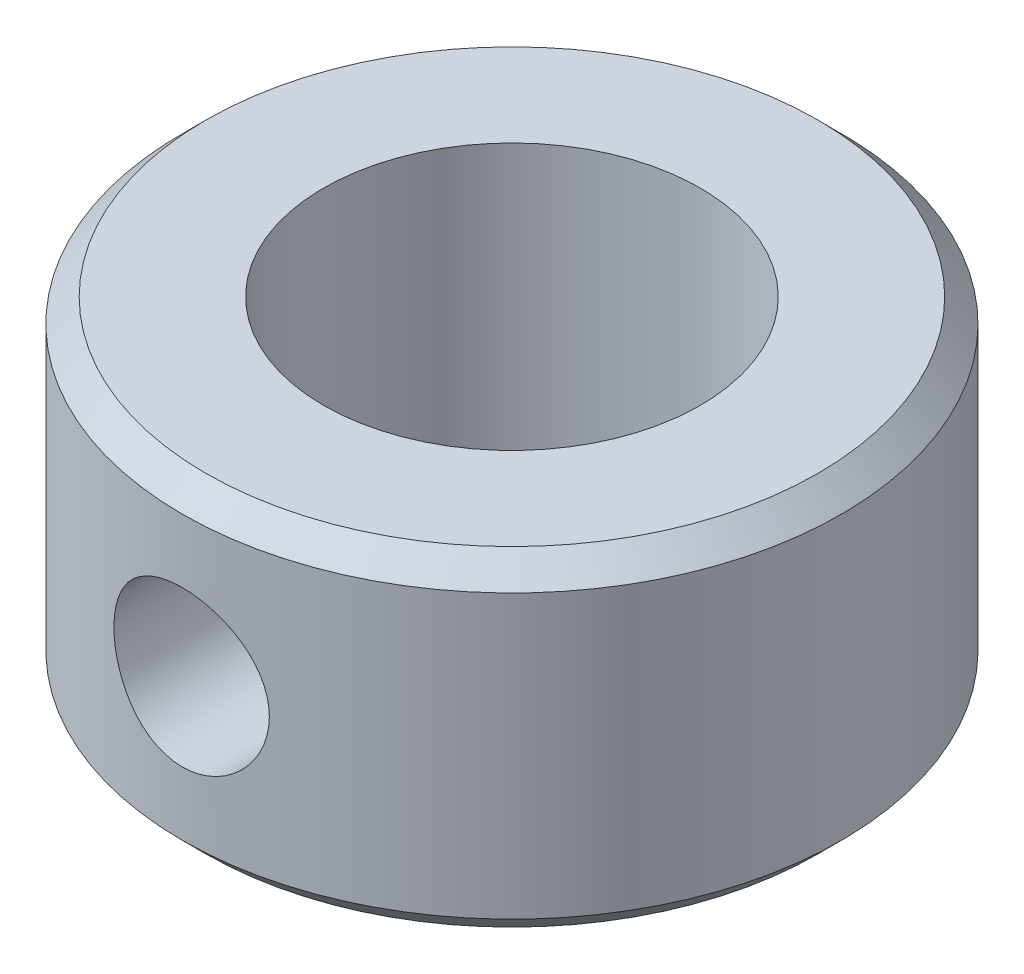
SolidWorks part; units mm, degrees
material "AISI 304"
ref_plane "Front Plane" through (0, 0, 0) normal (0, 0, 1) x (1, 0, 0)
ref_plane "Top Plane" through (0, 0, 0) normal (0, 1, 0) x (1, 0, 0)
ref_plane "Right Plane" through (0, 0, 0) normal (1, 0, 0) x (0, 0, -1)
sketch "Sketch1" plane through (0, 0, 0) normal (0, 1, 0) x (1, 0, 0)
  circle A0 centre (0, 0) radius 7
  circle A1 centre (0, 0) radius 4
  dimension "D1" = 8
  dimension "D2" = 14
extrude "Boss-Extrude1" add sketch "Sketch1" along normal mid plane 7
ref_plane "Plane1" through (0, 0, 7) normal (0, 0, 1) x (1, 0, 0)
hole_wizard "M4x0.7 Tapped Hole1" positions "Sketch2" profile "Sketch3" tap size "M4x0.7" standard "ANSI Metric"
sketch "Sketch2" plane through (0, 0, 7) normal (0, 0, 1) x (1, 0, 0)
  point P0 (0, 0)
sketch "Sketch3" plane through (0, 0, 7) normal (1, 0, 0) x (0, -1, 0)
  line L0 (0, 0) -> (0, 3)
  line L1 (0, 3) -> (1.65, 3)
  line L2 (1.65, 3) -> (1.65, 0)
  line L5 (1.65, 0) -> (0, 0)
  line L11 (0, -6.35) -> (0, 107.95) construction
  dimension "Thru Tap Drill Dia." = 3.3
  dimension "Thru Tap Drill Depth" = 3
cosmetic thread "Hole Thread1"
chamfer "Chamfer1" distance 0.5 angle 45 2 edges at (0, -3.5, 7) (0, 3.5, 7)
